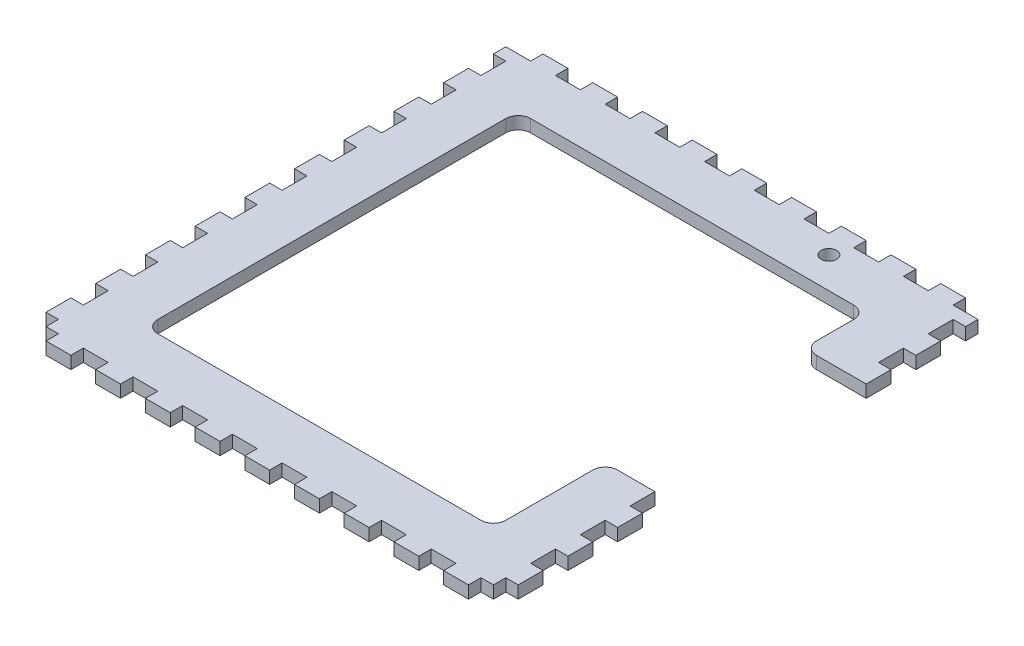
SolidWorks part; units mm, degrees
material "Pine"
ref_plane "Front Plane" through (0, 0, 0) normal (0, 0, 1) x (1, 0, 0)
ref_plane "Top Plane" through (0, 0, 0) normal (0, 1, 0) x (1, 0, 0)
ref_plane "Right Plane" through (0, 0, 0) normal (1, 0, 0) x (0, 0, -1)
sketch "Sketch1" plane through (0, 0, 0) normal (0, 1, 0) x (1, 0, 0)
  line L1 (0, 0) -> (241.3, 0)
  line L2 (0, 0) -> (0, 254)
  line L3 (0, 254) -> (241.3, 254)
  line L4 (241.3, 0) -> (241.3, 254)
  dimension "D1" = 241.3
  dimension "D2" = 254
extrude "Boss-Extrude1" add sketch "Sketch1" along normal blind 6.35
sketch "Sketch2" plane through (0, 6.35, 0) normal (0, 1, 0) x (1, 0, 0)
  line L1 (0, 12.7) -> (6.35, 12.7)
  line L2 (0, 12.7) -> (0, 0)
  line L3 (0, 0) -> (6.35, 0)
  line L4 (6.35, 12.7) -> (6.35, 0)
  line L5 (241.3, 12.7) -> (234.95, 12.7)
  line L6 (241.3, 12.7) -> (241.3, 0)
  line L7 (241.3, 0) -> (234.95, 0)
  line L8 (234.95, 12.7) -> (234.95, 0)
  dimension "D1" = 12.7
  dimension "D2" = 6.35
extrude "Cut-Extrude1" cut sketch "Sketch2" against normal through all
pattern_linear "LPattern1" count 10 spacing 25.4 along (0, 0, -1) of "Cut-Extrude1"
sketch "Sketch3" plane through (0, 6.35, 0) normal (0, 1, 0) x (1, 0, 0)
  line L0 (6.35, 0) -> (234.95, 0) construction
  line L1 (0, 0) -> (12.7, 0)
  line L2 (0, 0) -> (0, 6.35)
  line L3 (0, 6.35) -> (12.7, 6.35)
  line L4 (12.7, 0) -> (12.7, 6.35)
  line L5 (241.3, 254) -> (0, 254) construction
  line L6 (0, 254) -> (12.7, 254)
  line L7 (0, 254) -> (0, 247.65)
  line L8 (0, 247.65) -> (12.7, 247.65)
  line L9 (12.7, 254) -> (12.7, 247.65)
  dimension "D2" = 12.7
  dimension "D3" = 6.35
extrude "Cut-Extrude2" cut sketch "Sketch3" against normal through all
pattern_linear "LPattern2" count 10 spacing 25.4 along (1, 0, 0) of "Cut-Extrude2"
sketch "Sketch4" plane through (0, 6.35, 0) normal (0, 1, 0) x (1, 0, 0)
  line L0 (6.35, 177.8) -> (6.35, 190.5) construction
  line L1 (31.75, 222.25) -> (209.55, 222.25)
  line L2 (31.75, 222.25) -> (31.75, 31.75)
  line L3 (31.75, 31.75) -> (209.55, 31.75)
  line L4 (209.55, 222.25) -> (209.55, 31.75)
  line L5 (76.2, 247.65) -> (88.9, 247.65) construction
  line L6 (234.95, 190.5) -> (234.95, 177.8) construction
  line L7 (88.9, 6.35) -> (76.2, 6.35) construction
  dimension "D1" = 25.4
  dimension "D2" = 25.4
  dimension "D3" = 25.4
  dimension "D4" = 25.4
extrude "Cut-Extrude3" cut sketch "Sketch4" against normal through all
sketch "Sketch5" plane through (234.95, 0, 0) normal (1, 0, 0) x (0, 0, -1)
  line L1 (190.5, 6.35) -> (88.9, 6.35)
  line L2 (190.5, 6.35) -> (190.5, 0)
  line L3 (190.5, 0) -> (88.9, 0)
  line L4 (88.9, 6.35) -> (88.9, 0)
extrude "Cut-Extrude4" cut sketch "Sketch5" along normal through all and the other way blind 76.2
fillet "Fillet1" radius 6.35 6 edges at (209.55, 3.175, -222.25) (31.75, 3.175, -222.25) (31.75, 3.175, -31.75) (209.55, 3.175, -31.75) (209.55, 3.175, -88.9) (209.55, 3.175, -190.5)
sketch "Sketch6" plane through (0, -107.95, 0) normal (0, -1, 0) x (1, 0, 0)
  circle A0 centre (174.625, -238.125) radius 3.9687
  circle A1 centre (174.625, -238.125) radius 3.9688 construction
extrude "Cut-Extrude5" cut sketch "Sketch6" against normal through all
